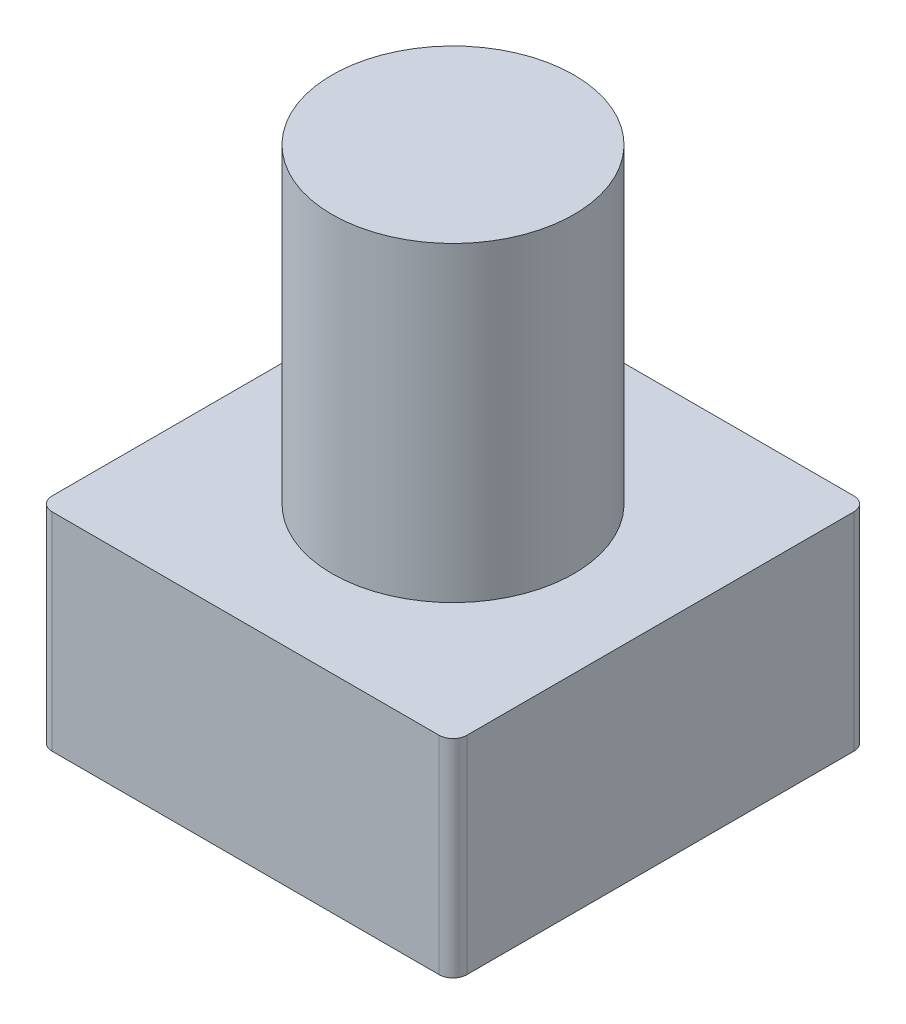
SolidWorks part; units mm, degrees
ref_plane "前视基准面" through (0, 0, 0) normal (0, 0, 1) x (1, 0, 0)
ref_plane "上视基准面" through (0, 0, 0) normal (0, 1, 0) x (1, 0, 0)
ref_plane "右视基准面" through (0, 0, 0) normal (1, 0, 0) x (0, 0, -1)
other "Configuration Table"
sketch "草图1" plane through (0, 0, 0) normal (0, 1, 0) x (1, 0, 0)
  line L1 (-2.8, -3) -> (2.8, -3)
  line L2 (-3, -2.8) -> (-3, 2.8)
  line L3 (-2.8, 3) -> (2.8, 3)
  line L4 (3, -2.8) -> (3, 2.8)
  line L5 (-3, -3) -> (3, 3) construction
  line L6 (-3, 3) -> (3, -3) construction
  arc A0 (2.8, -3) -> (3, -2.8) centre (2.8, -2.8) ccw
  arc A1 (-3, 2.8) -> (-2.8, 3) centre (-2.8, 2.8) cw
  arc A2 (-2.8, -3) -> (-3, -2.8) centre (-2.8, -2.8) cw
  arc A3 (2.8, 3) -> (3, 2.8) centre (2.8, 2.8) cw
  point P0 (0, 0)
  dimension "D3" = 0.2
  dimension "D1" = 6
  dimension "D2" = 6
extrude "凸台-拉伸1" add sketch "草图1" along normal blind 3
sketch "草图2" plane through (0, 3, 0) normal (0, 1, 0) x (1, 0, 0)
  circle A0 centre (0, 0) radius 1.75
  dimension "D1" = 3.5
extrude "凸台-拉伸2" add sketch "草图2" along normal blind 4.5
